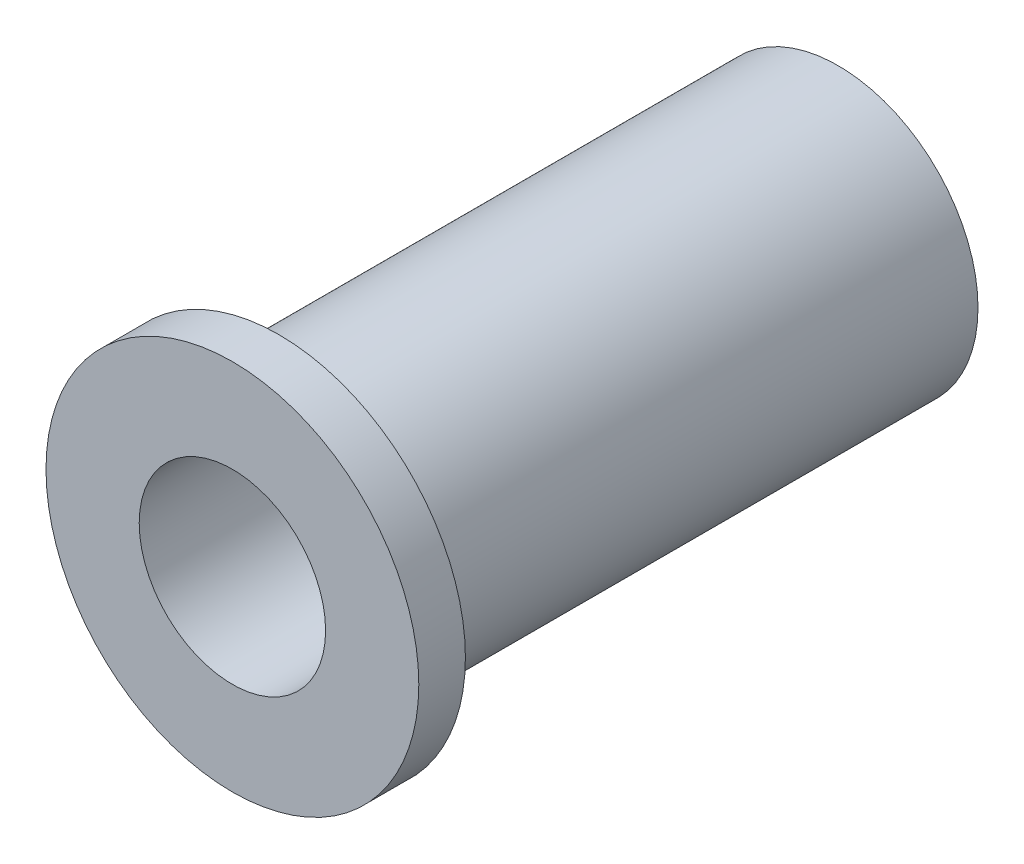
SolidWorks part; units mm, degrees
material "Aluminum Bronze"
ref_plane "Front Plane" through (0, 0, 0) normal (0, 0, 1) x (1, 0, 0)
ref_plane "Top Plane" through (0, 0, 0) normal (0, 1, 0) x (1, 0, 0)
ref_plane "Right Plane" through (0, 0, 0) normal (1, 0, 0) x (0, 0, -1)
sketch "Sketch1" plane through (0, 0, 0) normal (0, 0, 1) x (1, 0, 0)
  circle A0 centre (0, 0) radius 3.175
  circle A1 centre (0, 0) radius 4.7625
  dimension "D1" = 6.35
  dimension "D2" = 9.525
extrude "Boss-Extrude1" add sketch "Sketch1" along normal blind 19.05
sketch "Sketch2" plane through (0, 0, 19.05) normal (0, 0, 1) x (1, 0, 0)
  circle A0 centre (0, 0) radius 3.175
  circle A1 centre (0, 0) radius 3.175 construction
  circle A2 centre (0, 0) radius 6.35
  dimension "D1" = 12.7
extrude "Boss-Extrude2" add sketch "Sketch2" along normal blind 1.5875
